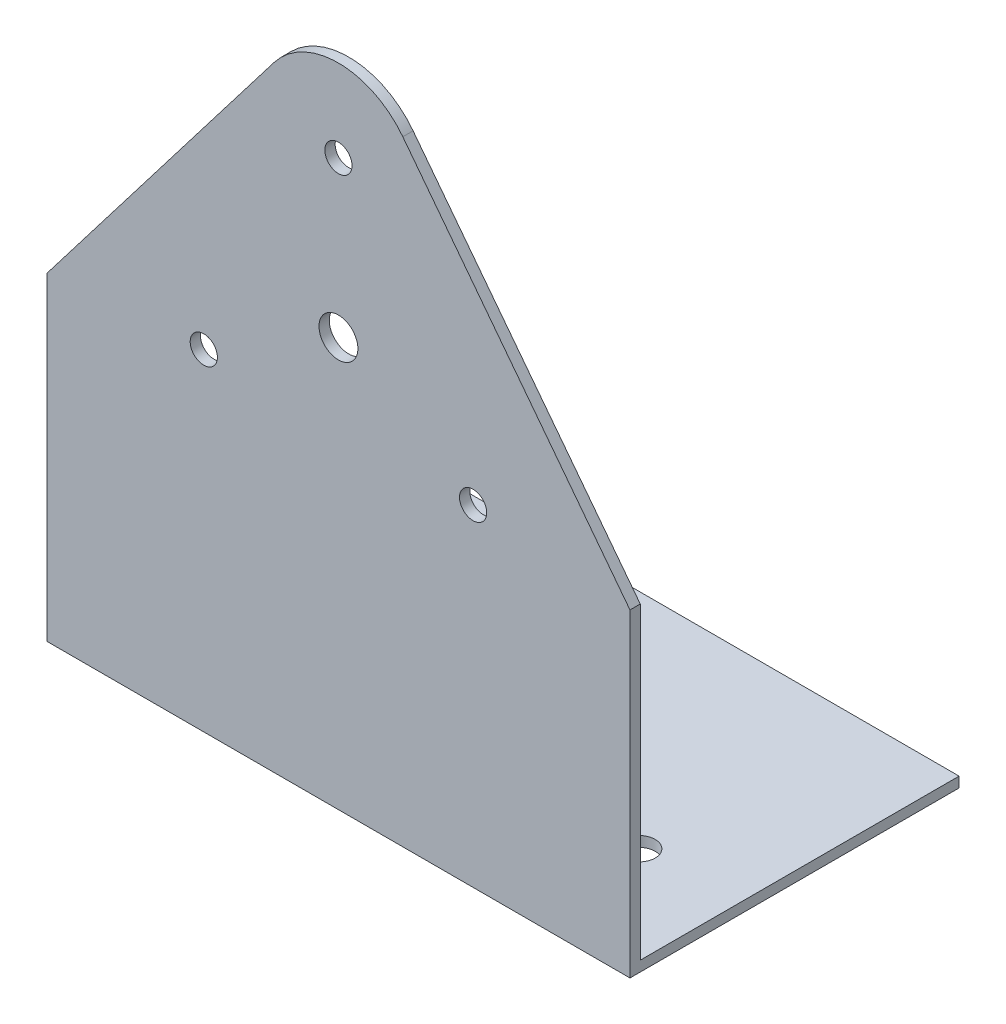
SolidWorks part; units mm, degrees
ref_plane "Front Plane" through (0, 0, 0) normal (0, 0, 1) x (1, 0, 0)
ref_plane "Top Plane" through (0, 0, 0) normal (0, 1, 0) x (1, 0, 0)
ref_plane "Right Plane" through (0, 0, 0) normal (1, 0, 0) x (0, 0, -1)
sketch "Sketch1" plane through (0, 0, 0) normal (1, 0, 0) x (0, 0, -1)
  line L2 (0, 0) -> (0, 100)
  line L3 (0, 100) -> (1.5875, 100)
  line L4 (1.5875, 1.5875) -> (1.5875, 100)
  line L5 (0, 0) -> (50.8, 0)
  line L7 (1.5875, 1.5875) -> (50.8, 1.5875)
  line L8 (50.8, 0) -> (50.8, 1.5875)
  dimension "D1" = 100
  dimension "D2" = 50.8
  dimension "D3" = 1.5875
extrude "Boss-Extrude1" add sketch "Sketch1" along normal blind 90
sketch "Sketch2" plane through (0, 0, 0) normal (0, 0, 1) x (1, 0, 0)
  line L0 (35.0644, 94.92) -> (0, 49.2)
  line L1 (0, 100) -> (0, 0) construction
  line L2 (54.9356, 94.92) -> (90, 49.2)
  line L3 (90, 100) -> (90, 0) construction
  line L5 (90, 0) -> (0, 0) construction
  line L7 (0, 49.2) -> (0, 100)
  line L8 (0, 100) -> (90, 100)
  line L9 (90, 49.2) -> (90, 100)
  arc A0 (54.9356, 94.92) -> (35.0644, 94.92) centre (45, 87.3) ccw
  point P14 (45, 0)
  dimension "D1" = 38.1
  dimension "D2" = 50.8
  dimension "D3" = 7.62
extrude "Cut-Extrude1" cut sketch "Sketch2" against normal through all
sketch "Sketch3" plane through (0, 0, 0) normal (0, 0, 1) x (1, 0, 0)
  line L0 (0, 0) -> (90, 0) construction
  circle A0 centre (45, 63.1212) radius 24 construction
  circle A2 centre (45, 87.1212) radius 2.1
  circle A5 centre (65.7846, 51.1212) radius 2.1
  arc A6 (54.9356, 94.92) -> (35.0644, 94.92) centre (45, 87.3) ccw construction
  circle A9 centre (24.2154, 51.1212) radius 2.1
  circle A10 centre (45, 63.1212) radius 3
  point P4 (45, 0)
  point P13 (45, 99.8212)
  point P21 (45, 63.1212)
  dimension "D1" = 48
  dimension "D2" = 4.2
  dimension "D4" = 12.7
  dimension "D5" = 6
  dimension "D3" = 3
extrude "Cut-Extrude2" cut sketch "Sketch3" against normal through all
sketch "Sketch4" plane through (0, 0, 0) normal (0, -1, 0) x (1, 0, 0)
  line L0 (15, -16.3875) -> (75, -16.3875) construction
  line L1 (0, 0) -> (90, 0) construction
  line L2 (90, 0) -> (0, 0) construction
  circle A0 centre (15, -16.3875) radius 2.5
  circle A1 centre (75, -16.3875) radius 2.5
  point P12 (45, -16.3875)
  point P13 (45, 0)
  dimension "D1" = 5
  dimension "D2" = 60
  dimension "D3" = 16.3875
extrude "Cut-Extrude3" cut sketch "Sketch4" against normal through all
